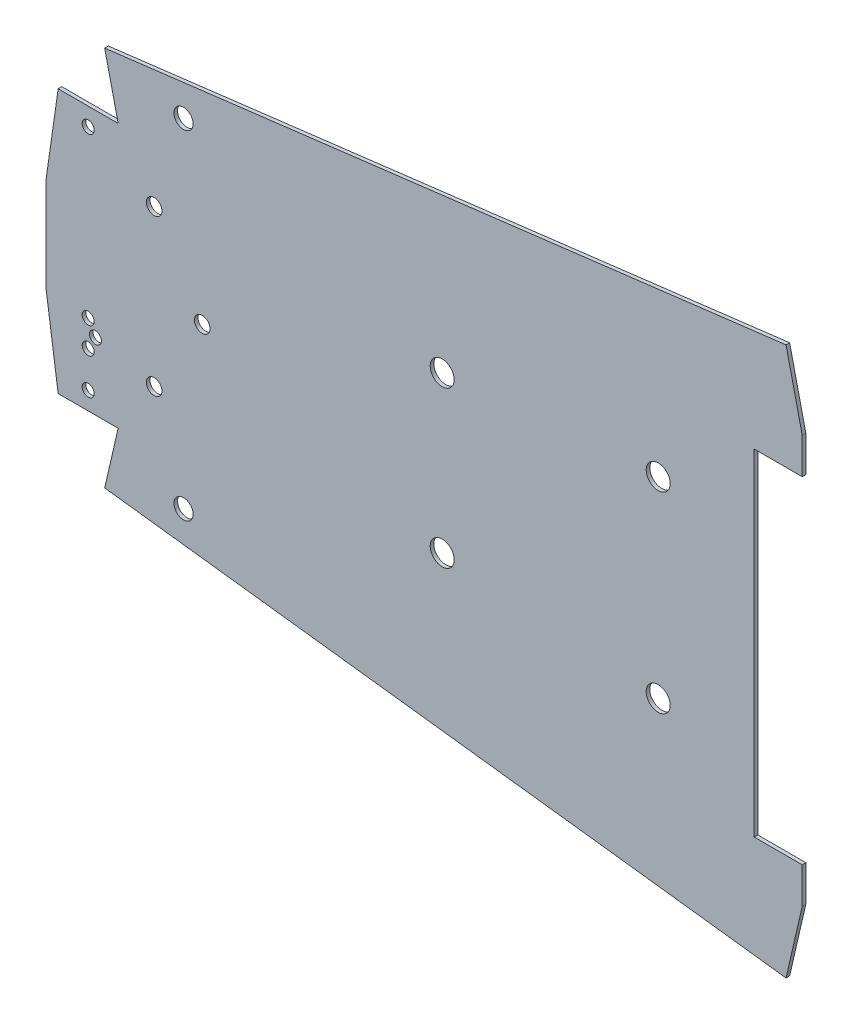
SolidWorks part; units mm, degrees
ref_plane "Ebene vorne" through (0, 0, 0) normal (0, 0, 1) x (1, 0, 0)
ref_plane "Ebene oben" through (0, 0, 0) normal (0, 1, 0) x (1, 0, 0)
ref_plane "Ebene rechts" through (0, 0, 0) normal (1, 0, 0) x (0, 0, -1)
sketch "Skizze1" plane through (0, 0, 0) normal (0, 0, 1) x (1, 0, 0)
  line L0 (-278.8148, 0) -> (274.1761, 0) construction
  line L1 (-216.0052, -55) -> (-216.0052, 55)
  line L2 (-216.0052, 55) -> (68.9948, 85)
  line L3 (68.9948, -85) -> (-216.0052, -55)
  line L4 (48.9948, 55) -> (48.9948, -55)
  line L5 (48.9948, 55) -> (48.9948, 70)
  line L6 (48.9948, -55) -> (48.9948, -70)
  line L7 (48.9948, 70) -> (68.9948, 70)
  line L8 (48.9948, -70) -> (68.9948, -70)
  line L9 (68.9948, 70) -> (68.9948, 85)
  line L10 (68.9948, -70) -> (68.9948, -85)
  line L11 (68.9948, -85) -> (62.2463, -114.2311)
  line L12 (68.9948, 85) -> (62.2463, 114.2311)
  line L13 (-216.0052, 55) -> (-221.6289, 79.3593)
  line L14 (-216.0052, -55) -> (-221.6289, -79.3593)
  line L15 (-221.6289, 79.3593) -> (62.2463, 114.2311)
  line L16 (62.2463, -114.2311) -> (-221.6289, -79.3593)
  line L17 (-216.0052, 55) -> (-241.0052, 55)
  line L18 (-216.0052, -55) -> (-241.0052, -55)
  line L21 (-246.0052, -20) -> (-246.0052, 20)
  line L22 (-246.0052, 20) -> (-241.0052, 55)
  line L23 (-246.0052, -20) -> (-241.0052, -55)
  circle A0 centre (8.9948, 40) radius 5
  circle A1 centre (8.9948, -40) radius 5
  circle A2 centre (-81.0052, 32.5) radius 5
  circle A3 centre (-81.0052, -32.5) radius 5
  circle A4 centre (-188.7795, 70.4349) radius 4
  circle A5 centre (-188.7795, -70.4349) radius 4
  circle A6 centre (-201.0052, 32.5) radius 3.25
  circle A7 centre (-201.0052, -32.5) radius 3.25
  circle A8 centre (-181.0052, 0) radius 3.25
  circle A9 centre (-228.5052, 47.5) radius 2.5
  circle A10 centre (-228.5052, -47.5) radius 2.5
  circle A11 centre (-228.5052, -32.5) radius 2.5
  circle A12 centre (-228.5052, -21.5) radius 2.5
  circle A13 centre (-225.5052, -27) radius 2.5
  point P6 (-216.0052, 0)
  point P9 (48.9948, 0)
  dimension "D14" = 10
  dimension "D15" = 10
  dimension "D16" = 8
  dimension "D19" = 15
  dimension "D21" = 95
  dimension "D23" = 15
  dimension "D25" = 3
  dimension "D27" = 5
  dimension "D1" = 110
  dimension "D2" = 285
  dimension "D3" = 25
  dimension "D4" = 140
  dimension "D5" = 170
  dimension "D6" = 40
  dimension "D7" = 25
  dimension "D8" = 40
  dimension "D9" = 90
  dimension "D10" = 65
  dimension "D11" = 80
  dimension "D12" = 20
  dimension "D13" = 30
  dimension "D17" = 12.5
  dimension "D18" = 30
  dimension "D20" = 20
  dimension "D22" = 12.5
  dimension "D24" = 11
  dimension "D26" = 5.5
extrude "Aufsatz-Linear austragen2" add sketch "Skizze1" along normal blind 1.5 and the other way blind 0.0001 contours L15 L13 L2 L12 A4 | L21 L0 L1 L17 L22 A9 | L0 L21 L23 L18 L1 A13 A12 A11 A10 | L1 L0 A8 L4 L5 L7 L9 L2 A6 A0 A2 | L0 L1 L3 L10 L8 L6 L4 A8 A3 A1 A7 | L16 L11 L3 L14 A5
